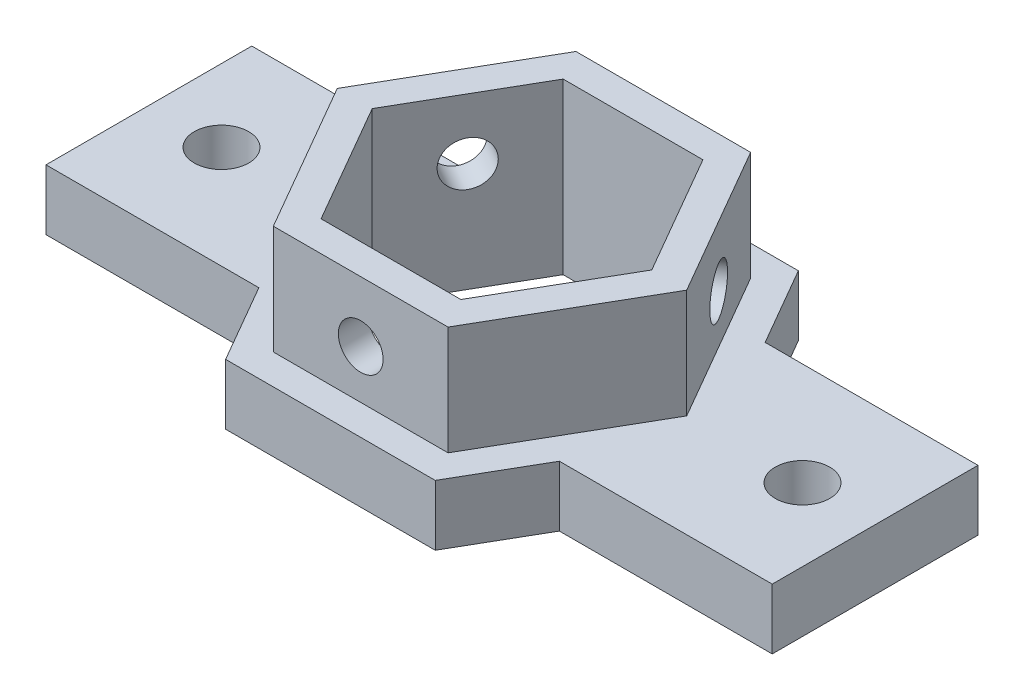
SolidWorks part; units mm, degrees
ref_plane "Front Plane" through (0, 0, 0) normal (0, 0, 1) x (1, 0, 0)
ref_plane "Top Plane" through (0, 0, 0) normal (0, 1, 0) x (1, 0, 0)
ref_plane "Right Plane" through (0, 0, 0) normal (1, 0, 0) x (0, 0, -1)
sketch "Sketch1" plane through (0, 0, 0) normal (0, 1, 0) x (1, 0, 0)
  line L0 (-12.3592, 8.5) -> (-30, 8.5)
  line L1 (30, -8.5) -> (12.3592, -8.5)
  line L2 (30, -8.5) -> (30, 8.5)
  line L3 (30, 8.5) -> (12.3592, 8.5)
  line L4 (-30, -8.5) -> (-30, 8.5)
  line L5 (30, -8.5) -> (-30, 8.5) construction
  line L6 (30, 8.5) -> (-30, -8.5) construction
  line L7 (-11.547, 0) -> (-5.7735, -10)
  line L8 (-5.7735, -10) -> (5.7735, -10)
  line L9 (5.7735, -10) -> (11.547, 0)
  line L10 (11.547, 0) -> (5.7735, 10)
  line L11 (5.7735, 10) -> (-5.7735, 10)
  line L12 (-5.7735, 10) -> (-11.547, 0)
  line L13 (-17.3205, 0) -> (-8.6603, -15)
  line L14 (-8.6603, -15) -> (8.6603, -15)
  line L15 (8.6603, -15) -> (17.3205, 0)
  line L16 (17.3205, 0) -> (8.6603, 15)
  line L17 (8.6603, 15) -> (-8.6603, 15)
  line L18 (-8.6603, 15) -> (-17.3205, 0)
  line L19 (-12.3592, -8.5) -> (-30, -8.5)
  circle A0 centre (0, 0) radius 10 construction
  circle A1 centre (0, 0) radius 15 construction
  point P0 (0, 0)
  dimension "D3" = 20
  dimension "D4" = 30
  dimension "D1" = 17
  dimension "D2" = 60
extrude "Boss-Extrude1" add sketch "Sketch1" along normal blind 5
sketch "Sketch3" plane through (0, 5, 0) normal (0, 1, 0) x (1, 0, 0)
  line L1 (-11.547, 0) -> (-5.7735, -10)
  line L2 (-5.7735, -10) -> (5.7735, -10)
  line L3 (5.7735, -10) -> (11.547, 0)
  line L4 (11.547, 0) -> (5.7735, 10)
  line L5 (5.7735, 10) -> (-5.7735, 10)
  line L6 (-5.7735, 10) -> (-11.547, 0)
  line L7 (-14.4338, 0) -> (-7.2169, -12.5)
  line L8 (-7.2169, -12.5) -> (7.2169, -12.5)
  line L9 (7.2169, -12.5) -> (14.4338, 0)
  line L10 (14.4338, 0) -> (7.2169, 12.5)
  line L11 (7.2169, 12.5) -> (-7.2169, 12.5)
  line L12 (-7.2169, 12.5) -> (-14.4338, 0)
  circle A0 centre (0, 0) radius 10 construction
  circle A1 centre (0, 0) radius 12.5 construction
  dimension "D1" = 20
  dimension "D2" = 25
extrude "Boss-Extrude2" add sketch "Sketch3" along normal blind 9
sketch "Sketch4" plane through (0, 5, 0) normal (0, 1, 0) x (1, 0, 0)
  circle A0 centre (-24, 0) radius 2.25
  dimension "D1" = 4.5
  dimension "D2" = 24
extrude "Cut-Extrude1" cut sketch "Sketch4" against normal through all
mirror "Mirror1" about plane through (0, 0, 0) normal (1, 0, 0) of "Cut-Extrude1"
sketch "Sketch5" plane through (0, 0, 15) normal (0, 0, 1) x (1, 0, 0)
  line L0 (7.2169, 14) -> (-7.2169, 14) construction
  circle A0 centre (0, 9) radius 1.85
  point P2 (0, 14)
  dimension "D1" = 3.7
  dimension "D2" = 5
extrude "Cut-Extrude2" cut sketch "Sketch5" against normal up to surface (5 mm away) up to face at (0, 7, 10)
sketch "Sketch6" plane through (12.9904, 0, -7.5) normal (0.866, 0, -0.5) x (-0.5, 0, -0.866)
  line L0 (-7.2169, 14) -> (7.2169, 14) construction
  circle A0 centre (0, 9) radius 2
  point P2 (0, 14)
  dimension "D1" = 4
  dimension "D2" = 5
extrude "Cut-Extrude3" cut sketch "Sketch6" against normal up to surface (5 mm away) up to face at (8.6603, 7, -5)
sketch "Sketch7" plane through (-12.9904, 0, -7.5) normal (-0.866, 0, -0.5) x (-0.5, 0, 0.866)
  line L1 (-7.2169, 14) -> (7.2169, 14) construction
  circle A0 centre (0, 9) radius 1.85
  point P2 (0, 14)
  dimension "D1" = 3.7
  dimension "D2" = 5
extrude "Cut-Extrude4" cut sketch "Sketch7" against normal up to surface (5 mm away) up to face at (-8.6603, 7, -5)
